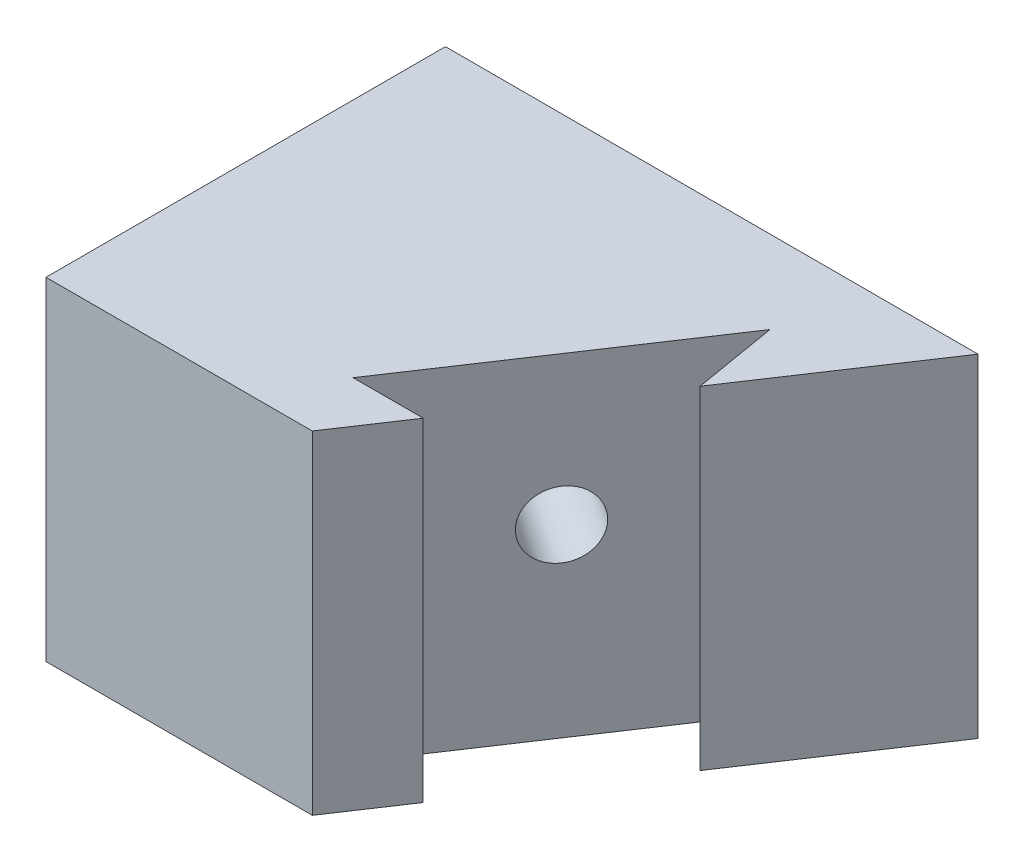
SolidWorks part; units mm, degrees
material "Plain Carbon Steel"
ref_plane "Front Plane" through (0, 0, 0) normal (0, 0, 1) x (1, 0, 0)
ref_plane "Top Plane" through (0, 0, 0) normal (0, 1, 0) x (1, 0, 0)
ref_plane "Right Plane" through (0, 0, 0) normal (1, 0, 0) x (0, 0, -1)
sketch "Sketch2" plane through (0, 0, 0) normal (0, 1, 0) x (1, 0, 0)
  line L1 (-40, 30) -> (40, 30)
  line L2 (-40, 30) -> (-40, -30)
  line L3 (-40, -30) -> (40, -30)
  line L4 (40, 30) -> (40, -30)
  line L5 (-40, 30) -> (40, -30) construction
  line L6 (-40, -30) -> (40, 30) construction
  point P0 (0, 0)
  dimension "D1" = 80
  dimension "D2" = 60
extrude "Boss-Extrude2" add sketch "Sketch2" along normal blind 50
sketch "Sketch3" plane through (0, 50, 0) normal (0, 1, 0) x (1, 0, 0)
  line L4 (40, -30) -> (40, 30)
  line L5 (40, 30) -> (-40, 30)
  line L6 (-40, 30) -> (-40, -30)
  line L7 (-40, -30) -> (40, -30)
  line L8 (40, -30) -> (40, 30)
  line L9 (40, 30) -> (-40, 30)
  line L10 (-40, 30) -> (-40, -30)
  line L11 (-40, -30) -> (40, -30)
  dimension "D1" = 0
sketch "Sketch4" plane through (0, 50, 0) normal (0, 1, 0) x (1, 0, 0)
  line L0 (0, -30) -> (40, 30)
  line L4 (40, -30) -> (40, 30)
  line L5 (40, 30) -> (-40, 30)
  line L6 (-40, 30) -> (-40, -30)
  line L7 (-40, -30) -> (40, -30)
  line L8 (40, -30) -> (40, 30)
  line L11 (0, -30) -> (40, -30)
  dimension "D1" = 0
extrude "Cut-Extrude1" cut sketch "Sketch4" against normal through all contours L8 L0 L11
ref_plane "Plane2" through (0, 0, 30) normal (0, 0, 1) x (1, 0, 0)
sketch "Sketch9" plane through (0, 50, 0) normal (0, 1, 0) x (1, 0, 0)
  line L0 (23.3077, 4.9615) -> (21.1779, 17.5738)
  line L1 (21.1779, 17.5738) -> (-3.8713, -20)
  line L2 (-3.8713, -20) -> (6.6667, -20)
  line L4 (-40, -30) -> (0, -30)
  line L5 (0, -30) -> (40, 30)
  line L6 (40, 30) -> (-40, 30)
  line L7 (-40, 30) -> (-40, -30)
  line L9 (6.6667, -20) -> (23.3077, 4.9615)
  dimension "D2" = 10
  dimension "D3" = 30
  dimension "D1" = 0
extrude "Cut-Extrude3" cut sketch "Sketch9" against normal through all
sketch "Sketch10" plane through (6.5506, 0, 4.3671) normal (0.8321, 0, 0.5547) x (0.5547, 0, -0.8321)
  line L4 (26.3697, 50) -> (-18.7884, 50)
  line L5 (-18.7884, 50) -> (-18.7884, 0)
  line L6 (-18.7884, 0) -> (26.3697, 0)
  line L7 (26.3697, 0) -> (26.3697, 50)
  line L8 (26.3697, 50) -> (-18.7884, 50)
  line L9 (-18.7884, 50) -> (-18.7884, 0)
  line L10 (-18.7884, 0) -> (26.3697, 0)
  line L11 (26.3697, 0) -> (26.3697, 50)
  circle A0 centre (3.7907, 27.7575) radius 5
  point P6 (3.7907, 50)
  dimension "D2" = 10
  dimension "D1" = 0
extrude "Cut-Extrude4" cut sketch "Sketch10" against normal through all contours A0
sketch "Sketch11" plane through (0, 0, 0) normal (0, 1, 0) x (1, 0, 0)
  line L8 (6.6667, -20) -> (-3.8713, -20)
  line L9 (-3.8713, -20) -> (21.1779, 17.5738)
  line L10 (21.1779, 17.5738) -> (23.3077, 4.9615)
  line L11 (23.3077, 4.9615) -> (40, 30)
  line L12 (40, 30) -> (-40, 30)
  line L13 (-40, 30) -> (-40, -30)
  line L14 (-40, -30) -> (0, -30)
  line L15 (0, -30) -> (6.6667, -20)
  line L16 (6.6667, -20) -> (-3.8713, -20)
  line L17 (-3.8713, -20) -> (21.1779, 17.5738)
  line L18 (21.1779, 17.5738) -> (23.3077, 4.9615)
  line L19 (23.3077, 4.9615) -> (40, 30)
  line L20 (40, 30) -> (-40, 30)
  line L21 (-40, 30) -> (-40, -30)
  line L22 (-40, -30) -> (0, -30)
  line L23 (0, -30) -> (6.6667, -20)
  dimension "D1" = 0
